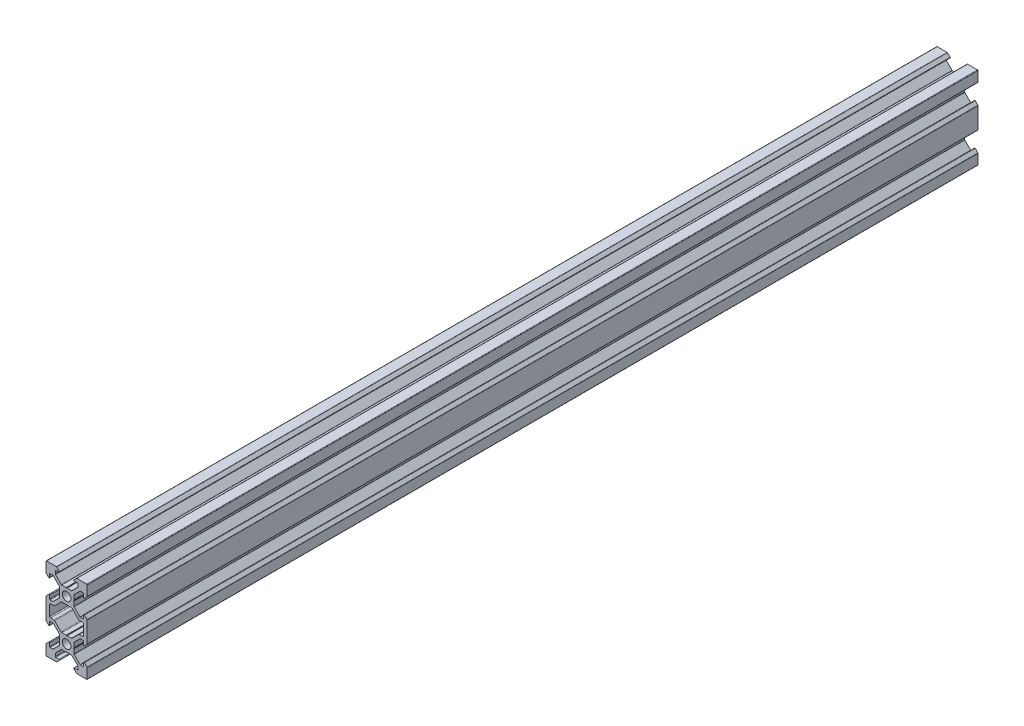
SolidWorks part; units mm, degrees
ref_plane "Front Plane" through (0, 0, 0) normal (0, 0, 1) x (1, 0, 0)
ref_plane "Top Plane" through (0, 0, 0) normal (0, 1, 0) x (1, 0, 0)
ref_plane "Right Plane" through (0, 0, 0) normal (1, 0, 0) x (0, 0, -1)
sketch "Sketch1" plane through (0, 0, 0) normal (0, 0, 1) x (1, 0, 0)
  line L0 (3.5607, 3.5607) -> (10.6317, 10.6317) construction
  line L1 (2.5, -3.5607) -> (-2.5, -3.5607)
  line L2 (3.5607, -2.5) -> (3.5607, 2.5)
  line L3 (2.5, 3.5607) -> (-2.5, 3.5607)
  line L4 (-3.5607, -2.5) -> (-3.5607, 2.5)
  line L5 (3.5607, -3.5607) -> (-3.5607, 3.5607) construction
  line L6 (3.5607, 3.5607) -> (-3.5607, -3.5607) construction
  line L7 (2.5, 3.5607) -> (5.5, 6.5607)
  line L8 (5.5, 6.5607) -> (5.5, 8.2521)
  line L9 (5.5, 8.2521) -> (3.1, 8.2521)
  line L10 (3.1, 8.2521) -> (4.8479, 10)
  line L11 (4.8479, 10) -> (10, 10)
  line L12 (3.5607, 2.5) -> (6.5607, 5.5)
  line L13 (6.5607, 5.5) -> (8.2521, 5.5)
  line L14 (8.2521, 5.5) -> (8.2521, 3.1)
  line L15 (8.2521, 3.1) -> (10, 4.8479)
  line L16 (10, 4.8479) -> (10, 10)
  line L17 (0, -55) -> (0, 55) construction
  line L18 (-3.5607, 3.5607) -> (-10.6317, 10.6317) construction
  line L19 (-10, 4.8479) -> (-10, 10)
  line L20 (-8.2521, 3.1) -> (-10, 4.8479)
  line L21 (-8.2521, 5.5) -> (-8.2521, 3.1)
  line L22 (-6.5607, 5.5) -> (-8.2521, 5.5)
  line L23 (-3.5607, 2.5) -> (-6.5607, 5.5)
  line L24 (-4.8479, 10) -> (-10, 10)
  line L25 (-3.1, 8.2521) -> (-4.8479, 10)
  line L26 (-5.5, 8.2521) -> (-3.1, 8.2521)
  line L27 (-5.5, 6.5607) -> (-5.5, 8.2521)
  line L28 (-2.5, 3.5607) -> (-5.5, 6.5607)
  line L29 (-8.2521, -7) -> (-5.9393, -7)
  line L30 (55, 0) -> (-55, 0) construction
  line L31 (-3.5607, -3.5607) -> (-10.6317, -10.6317) construction
  line L32 (3.5607, -3.5607) -> (10.6317, -10.6317) construction
  line L33 (-2.5, -3.5607) -> (-5.5, -6.5607)
  line L34 (-5.5, -6.5607) -> (-5.9393, -7)
  line L35 (5.5, -6.5607) -> (5.9393, -7)
  line L36 (8.2521, -7) -> (5.9393, -7)
  line L37 (-12.2633, -10) -> (14.5346, -10) construction
  line L38 (-3.5607, -2.5) -> (-6.5607, -5.5)
  line L39 (-6.5607, -5.5) -> (-8.2521, -5.5)
  line L40 (-8.2521, -5.5) -> (-8.2521, -3.1)
  line L41 (-8.2521, -3.1) -> (-10, -4.8479)
  line L42 (-10, -4.8479) -> (-10, -7)
  line L43 (10, -4.8479) -> (10, -7)
  line L44 (8.2521, -3.1) -> (10, -4.8479)
  line L45 (8.2521, -5.5) -> (8.2521, -3.1)
  line L46 (6.5607, -5.5) -> (8.2521, -5.5)
  line L47 (3.5607, -2.5) -> (6.5607, -5.5)
  line L48 (-3.5607, -23.5607) -> (-10.6317, -30.6317) construction
  line L49 (3.5607, -23.5607) -> (-3.5607, -16.4393) construction
  line L50 (3.5607, -16.4393) -> (-3.5607, -23.5607) construction
  line L51 (3.5607, -23.5607) -> (10.6317, -30.6317) construction
  line L52 (2.5, -3.5607) -> (5.5, -6.5607)
  line L53 (2.5, -16.4393) -> (5.5, -13.4393)
  line L54 (3.5607, -17.5) -> (6.5607, -14.5)
  line L55 (6.5607, -14.5) -> (8.2521, -14.5)
  line L56 (8.2521, -14.5) -> (8.2521, -16.9)
  line L57 (8.2521, -16.9) -> (10, -15.1521)
  line L58 (10, -15.1521) -> (10, -13)
  line L59 (-10, -15.1521) -> (-10, -13)
  line L60 (-8.2521, -16.9) -> (-10, -15.1521)
  line L61 (-8.2521, -14.5) -> (-8.2521, -16.9)
  line L62 (-6.5607, -14.5) -> (-8.2521, -14.5)
  line L63 (-3.5607, -17.5) -> (-6.5607, -14.5)
  line L64 (8.2521, -13) -> (5.9393, -13)
  line L65 (5.5, -13.4393) -> (5.9393, -13)
  line L66 (-5.5, -13.4393) -> (-5.9393, -13)
  line L67 (-2.5, -16.4393) -> (-5.5, -13.4393)
  line L68 (-8.2521, -13) -> (-5.9393, -13)
  line L69 (-2.5, -23.5607) -> (-5.5, -26.5607)
  line L70 (-5.5, -26.5607) -> (-5.5, -28.2521)
  line L71 (-5.5, -28.2521) -> (-3.1, -28.2521)
  line L72 (-3.1, -28.2521) -> (-4.8479, -30)
  line L73 (-4.8479, -30) -> (-10, -30)
  line L74 (-3.5607, -22.5) -> (-6.5607, -25.5)
  line L75 (-6.5607, -25.5) -> (-8.2521, -25.5)
  line L76 (-8.2521, -25.5) -> (-8.2521, -23.1)
  line L77 (-8.2521, -23.1) -> (-10, -24.8479)
  line L78 (-10, -24.8479) -> (-10, -30)
  line L79 (10, -24.8479) -> (10, -30)
  line L80 (8.2521, -23.1) -> (10, -24.8479)
  line L81 (8.2521, -25.5) -> (8.2521, -23.1)
  line L82 (6.5607, -25.5) -> (8.2521, -25.5)
  line L83 (3.5607, -22.5) -> (6.5607, -25.5)
  line L84 (4.8479, -30) -> (10, -30)
  line L85 (3.1, -28.2521) -> (4.8479, -30)
  line L86 (5.5, -28.2521) -> (3.1, -28.2521)
  line L87 (5.5, -26.5607) -> (5.5, -28.2521)
  line L88 (2.5, -23.5607) -> (5.5, -26.5607)
  line L89 (-3.5607, -17.5) -> (-3.5607, -22.5)
  line L90 (2.5, -23.5607) -> (-2.5, -23.5607)
  line L91 (3.5607, -17.5) -> (3.5607, -22.5)
  line L92 (2.5, -16.4393) -> (-2.5, -16.4393)
  line L93 (-10, -7) -> (-10, -13)
  line L94 (-8.2521, -13) -> (-8.2521, -7)
  line L95 (8.2521, -13) -> (8.2521, -7)
  line L96 (10, -7) -> (10, -13)
  circle A0 centre (0, 0) radius 2.1
  circle A1 centre (0, -20) radius 2.1
  point P0 (0, 0)
  point P102 (0, -20)
  dimension "D10" = 4.2
  dimension "D11" = 4.2
  dimension "D1" = 1.5
  dimension "D2" = 10
  dimension "D3" = 20
  dimension "D4" = 6.2
  dimension "D5" = 11
  dimension "D6" = 45
  dimension "D7" = 1.5
  dimension "D8" = 10
  dimension "D9" = 5
extrude "Boss-Extrude1" add sketch "Sketch1" along normal blind 432
fillet "Fillet1" radius 0.25 64 edges at (5.5, 6.5607, 216) (5.5, 8.2521, 216) (3.1, 8.2521, 216) (4.8479, 10, 216) (10, 10, 216) (10, 4.8479, 216) (8.2521, 3.1, 216) (8.2521, 5.5, 216) (6.5607, 5.5, 216) (3.5607, 2.5, 216) (3.5607, -2.5, 216) (6.5607, -5.5, 216) (8.2521, -5.5, 216) (8.2521, -3.1, 216) (10, -4.8479, 216) (10, -15.1521, 216) (8.2521, -16.9, 216) (8.2521, -14.5, 216) (6.5607, -14.5, 216) (3.5607, -17.5, 216) (3.5607, -22.5, 216) (6.5607, -25.5, 216) (8.2521, -25.5, 216) (8.2521, -23.1, 216) (10, -24.8479, 216) (10, -30, 216) (4.8479, -30, 216) (3.1, -28.2521, 216) (5.5, -28.2521, 216) (5.5, -26.5607, 216) (2.5, -23.5607, 216) (-2.5, -23.5607, 216) (-5.5, -26.5607, 216) (-5.5, -28.2521, 216) (-3.1, -28.2521, 216) (-4.8479, -30, 216) (-10, -30, 216) (-10, -24.8479, 216) (-8.2521, -23.1, 216) (-8.2521, -25.5, 216) (-6.5607, -25.5, 216) (-3.5607, -22.5, 216) (-3.5607, -17.5, 216) (-6.5607, -14.5, 216) (-8.2521, -14.5, 216) (-8.2521, -16.9, 216) (-10, -15.1521, 216) (-10, -4.8479, 216) (-8.2521, -3.1, 216) (-8.2521, -5.5, 216) (-6.5607, -5.5, 216) (-3.5607, -2.5, 216) (-3.5607, 2.5, 216) (-6.5607, 5.5, 216) (-8.2521, 5.5, 216) (-8.2521, 3.1, 216) (-10, 4.8479, 216) (-10, 10, 216) (-4.8479, 10, 216) (-5.5, 8.2521, 216) (-5.5, 6.5607, 216) (-2.5, 3.5607, 216) (2.5, 3.5607, 216) (-3.1, 8.2521, 216)
fillet "Fillet2" radius 0.5 12 edges at (-5.9393, -7, 216) (-8.2521, -7, 216) (-8.2521, -13, 216) (-5.9393, -13, 216) (-2.5, -16.4393, 216) (2.5, -16.4393, 216) (8.2521, -7, 216) (5.9393, -7, 216) (2.5, -3.5607, 216) (-2.5, -3.5607, 216) (5.9393, -13, 216) (8.2521, -13, 216)
sketch "Sketch2" plane through (0, 0, 432) normal (0, 0, 1) x (1, 0, 0)
  line L4 (0, 3.5607) -> (0, 3.1447) construction
  line L5 (2.3964, 3.5607) -> (-2.3964, 3.5607) construction
  line L6 (0, 3.399) -> (-0.2423, 3.5607)
  line L7 (0, 3.399) -> (0.2423, 3.5607)
  line L8 (-0.2423, 3.5607) -> (0.2423, 3.5607)
  line L9 (55, 0) -> (-55, 0) construction
  line L10 (0, -3.5607) -> (0, -3.1447) construction
  line L11 (0, -3.399) -> (0.2423, -3.5607)
  line L12 (0, -3.399) -> (-0.2423, -3.5607)
  line L13 (-0.2423, -3.5607) -> (0.2423, -3.5607)
  line L14 (0, 0) -> (-4.0856, 4.0856) construction
  line L15 (-8.2521, -10) -> (4.1581, -10) construction
  line L16 (-8.2521, -7.5) -> (-8.2521, -12.5) construction
  line L17 (3.5607, 0) -> (3.1447, 0) construction
  line L18 (3.5607, 0.2423) -> (3.5607, -0.2423)
  line L19 (3.399, 0) -> (3.5607, 0.2423)
  line L20 (3.399, 0) -> (3.5607, -0.2423)
  line L21 (-3.5607, 0) -> (-3.1447, 0) construction
  line L22 (-3.5607, 0.2423) -> (-3.5607, -0.2423)
  line L23 (-3.399, 0) -> (-3.5607, -0.2423)
  line L24 (-3.399, 0) -> (-3.5607, 0.2423)
  line L25 (-3.5607, -20) -> (-3.1447, -20) construction
  line L26 (3.5607, -20) -> (3.1447, -20) construction
  line L27 (0, -20) -> (-4.0856, -24.0856) construction
  line L28 (0, -16.4393) -> (0, -16.8553) construction
  line L29 (0, -23.5607) -> (0, -23.1447) construction
  line L30 (-3.399, -20) -> (-3.5607, -20.2423)
  line L31 (-3.399, -20) -> (-3.5607, -19.7577)
  line L32 (-3.5607, -20.2423) -> (-3.5607, -19.7577)
  line L33 (3.399, -20) -> (3.5607, -19.7577)
  line L34 (3.399, -20) -> (3.5607, -20.2423)
  line L35 (3.5607, -20.2423) -> (3.5607, -19.7577)
  line L36 (-0.2423, -16.4393) -> (0.2423, -16.4393)
  line L37 (0, -16.601) -> (-0.2423, -16.4393)
  line L38 (0, -16.601) -> (0.2423, -16.4393)
  line L39 (-0.2423, -23.5607) -> (0.2423, -23.5607)
  line L40 (0, -23.399) -> (0.2423, -23.5607)
  line L41 (0, -23.399) -> (-0.2423, -23.5607)
extrude "Cut-Extrude1" cut sketch "Sketch2" against normal through all
